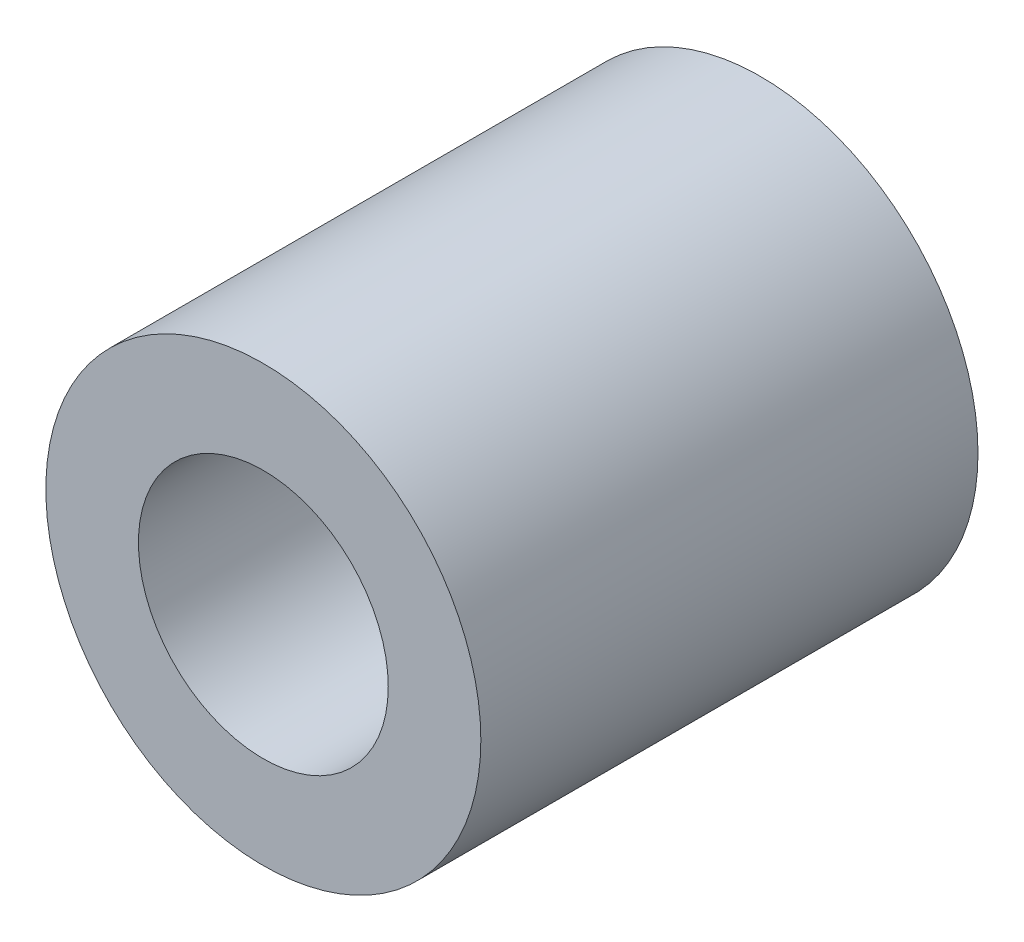
SolidWorks part; units mm, degrees
ref_plane "Plan de face" through (0, 0, 0) normal (0, 0, 1) x (1, 0, 0)
ref_plane "Plan de dessus" through (0, 0, 0) normal (0, 1, 0) x (1, 0, 0)
ref_plane "Plan de droite" through (0, 0, 0) normal (1, 0, 0) x (0, 0, -1)
sketch "Esquisse1" plane through (0, 0, 0) normal (0, 0, 1) x (1, 0, 0)
  circle A0 centre (0, 0) radius 10.05
  circle A1 centre (0, 0) radius 17.5
  dimension "D1" = 20.1
  dimension "D2" = 35
extrude "Boss.-Extru.1" add sketch "Esquisse1" along normal blind 40
sketch "Esquisse2" plane through (0, 0, 0) normal (0, 1, 0) x (1, 0, 0)
  circle A0 centre (0, -20.7539) radius 2.5
  dimension "D1" = 5
extrude "Enlèv. mat.-Extru.1" [suppressed] cut sketch "Esquisse2" against normal blind 40
sketch "Esquisse3" plane through (0, 0, 0) normal (1, 0, 0) x (0, 0, -1)
  line L0 (0, -17.5) -> (0, 17.5) construction
  circle A0 centre (-20, 0) radius 2.5
  dimension "D2" = 5
  dimension "D1" = 20
extrude "Enlèv. mat.-Extru.2" [suppressed] cut sketch "Esquisse3" against normal blind 40
